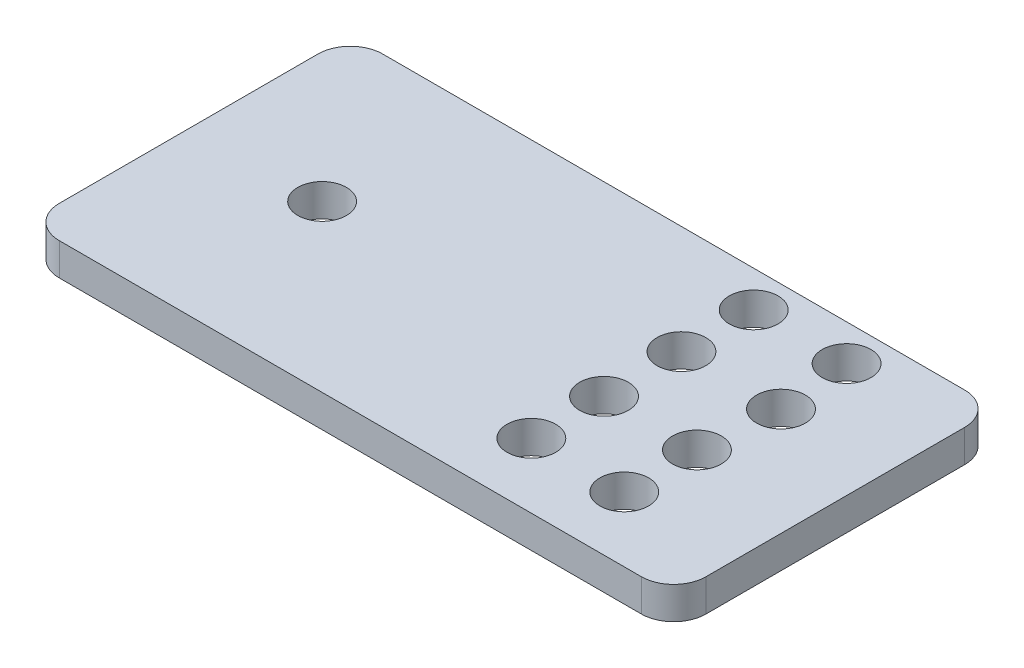
SolidWorks part; units mm, degrees
ref_plane "Front Plane" through (0, 0, 0) normal (0, 0, 1) x (1, 0, 0)
ref_plane "Top Plane" through (0, 0, 0) normal (0, 1, 0) x (1, 0, 0)
ref_plane "Right Plane" through (0, 0, 0) normal (1, 0, 0) x (0, 0, -1)
sketch "Sketch1" plane through (0, 0, 0) normal (0, 1, 0) x (1, 0, 0)
  line L1 (73.5622, 48.8525) -> (-106.4378, 48.8525)
  line L2 (83.5622, 38.8525) -> (83.5622, -41.1475)
  line L3 (73.5622, -51.1475) -> (-106.4378, -51.1475)
  line L4 (-116.4378, 38.8525) -> (-116.4378, -41.1475)
  arc A0 (73.5622, 48.8525) -> (83.5622, 38.8525) centre (73.5622, 38.8525) cw
  arc A1 (83.5622, -41.1475) -> (73.5622, -51.1475) centre (73.5622, -41.1475) cw
  arc A2 (-106.4378, 48.8525) -> (-116.4378, 38.8525) centre (-106.4378, 38.8525) ccw
  arc A3 (-116.4378, -41.1475) -> (-106.4378, -51.1475) centre (-106.4378, -41.1475) ccw
  point P6 (83.5622, 48.8525)
  point P9 (83.5622, -51.1475)
  point P12 (-116.4378, 48.8525)
  dimension "D3" = 10
  dimension "D1" = 200
  dimension "D2" = 100
extrude "Boss-Extrude1" add sketch "Sketch1" along normal blind 10
sketch "Sketch3" plane through (0, 0, 0) normal (0, 1, 0) x (1, 0, 0)
  circle A0 centre (48.2156, 37.6787) radius 7.5353
  circle A1 centre (19.4808, 37.6787) radius 7.5353
  circle A2 centre (48.2156, -31.0797) radius 7.5353
  circle A3 centre (19.4808, -31.0797) radius 7.5353
  circle A4 centre (-76.302, 0) radius 7.5353
  circle A5 centre (19.4808, -8.6069) radius 7.5353
  circle A6 centre (48.2156, -8.6069) radius 7.5353
  circle A7 centre (19.4808, 15.3388) radius 7.5353
  circle A8 centre (50.2681, 15.3388) radius 7.5353
extrude "Cut-Extrude10" cut sketch "Sketch3" along normal blind 10
